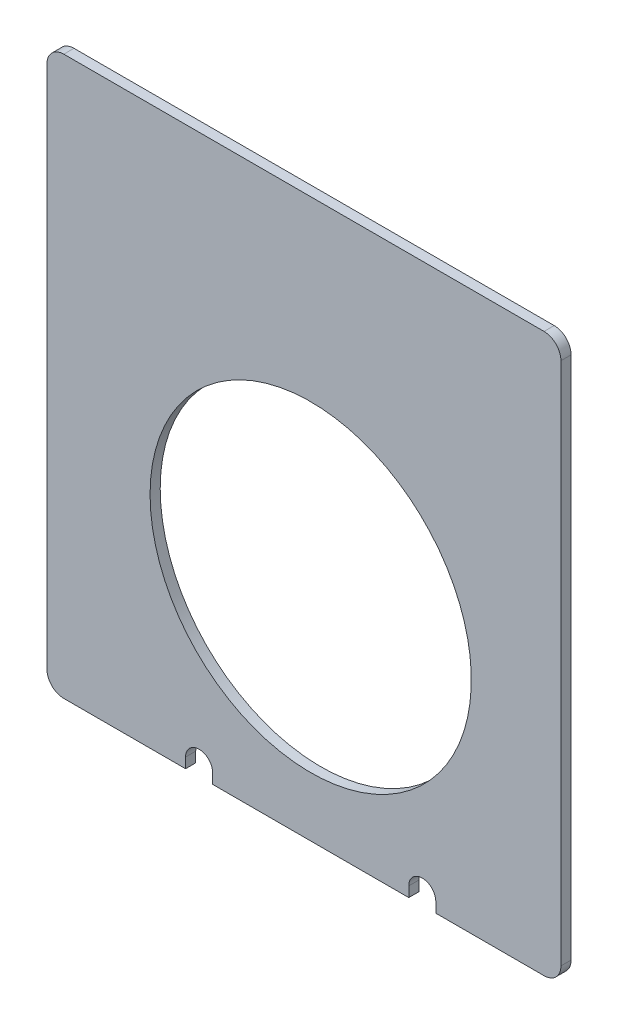
SolidWorks part; units mm, degrees
ref_plane "Face" through (0, 0, 0) normal (0, 0, 1) x (1, 0, 0)
ref_plane "Dessus" through (0, 0, 0) normal (0, 1, 0) x (1, 0, 0)
ref_plane "Droite" through (0, 0, 0) normal (1, 0, 0) x (0, 0, -1)
sketch "Esquisse1" plane through (0, 0, 0) normal (0, 0, 1) x (1, 0, 0)
  line L1 (0, 0) -> (-152, 0)
  line L2 (0, 0) -> (0, 165)
  line L3 (0, 165) -> (-152, 165)
  line L4 (-152, 0) -> (-152, 165)
  dimension "D1" = 152
  dimension "D2" = 165
extrude "Boss.-Extru.1" add sketch "Esquisse1" along normal blind 3
fillet "Congé1" radius 5 4 edges at (0, 0, 1.5) (-152, 0, 1.5) (-152, 165, 1.5) (0, 165, 1.5)
sketch "Esquisse2" plane through (0, 0, 0) normal (0, 0, -1) x (-1, 0, 0)
  line L0 (147, 0) -> (5, 0) construction
  line L1 (152, 160) -> (152, 5) construction
  circle A0 centre (74, 65) radius 47.5
  dimension "D1" = 95
  dimension "D2" = 65
  dimension "D3" = 78
extrude "Enlèv. mat.-Extru.1" cut sketch "Esquisse2" against normal blind 3
sketch "Esquisse3" plane through (0, 0, 0) normal (0, 0, -1) x (-1, 0, 0)
  line L0 (147, 0) -> (5, 0) construction
  line L2 (41, -3) -> (41, 3) construction
  line L3 (37, -3) -> (37, 3)
  line L4 (45, -3) -> (45, 3)
  line L5 (107, -3) -> (107, 3) construction
  line L6 (103, -3) -> (103, 3)
  line L7 (111, -3) -> (111, 3)
  line L8 (0, 5) -> (0, 160) construction
  line L9 (152, 160) -> (152, 5) construction
  arc A0 (37, -3) -> (45, -3) centre (41, -3) ccw
  arc A2 (45, 3) -> (37, 3) centre (41, 3) ccw
  arc A3 (103, -3) -> (111, -3) centre (107, -3) ccw
  arc A4 (111, 3) -> (103, 3) centre (107, 3) ccw
  point P6 (41, 0)
  point P12 (107, 0)
  dimension "D1" = 8
  dimension "D2" = 8
  dimension "D3" = 6
  dimension "D4" = 6
  dimension "D5" = 41
  dimension "D6" = 45
extrude "Enlèv. mat.-Extru.2" cut sketch "Esquisse3" against normal blind 3
